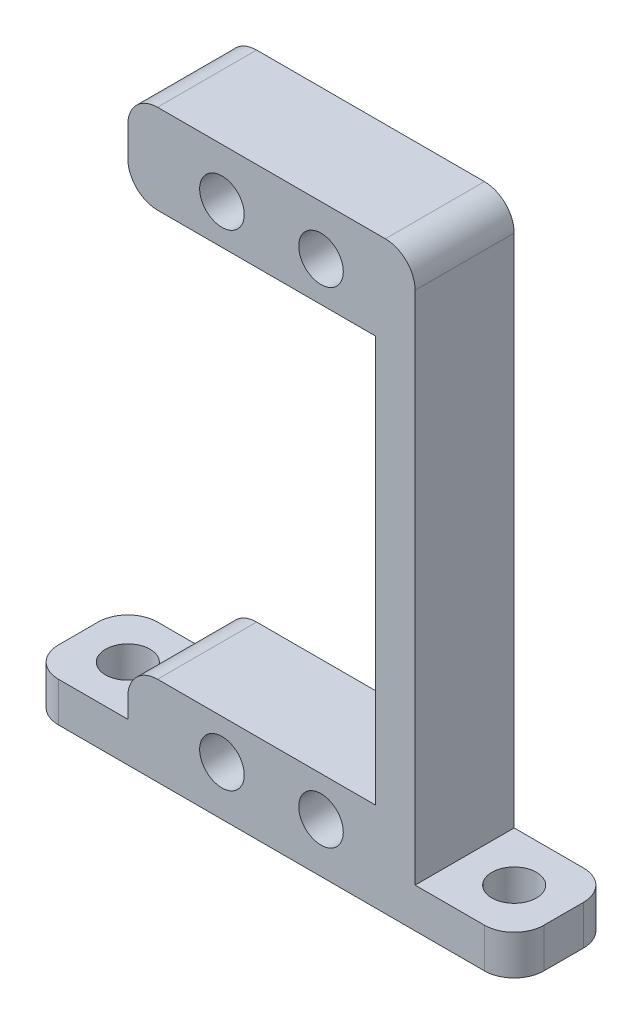
SolidWorks part; units mm, degrees
material "8200树脂"
ref_plane "前视基准面" through (0, 0, 0) normal (0, 0, 1) x (1, 0, 0)
ref_plane "上视基准面" through (0, 0, 0) normal (0, 1, 0) x (1, 0, 0)
ref_plane "右视基准面" through (0, 0, 0) normal (1, 0, 0) x (0, 0, -1)
sketch "草图1" plane through (0, 0, 0) normal (0, 0, 1) x (1, 0, 0)
  line L0 (-10.5, 20.5) -> (-14.5, 20.5)
  line L1 (-10.5, -20.5) -> (10.5, -20.5)
  line L2 (-10.5, -20.5) -> (-10.5, 20.5)
  line L3 (-10.5, 20.5) -> (10.5, 20.5)
  line L4 (10.5, -20.5) -> (10.5, 20.5)
  line L5 (-10.5, -20.5) -> (10.5, 20.5) construction
  line L6 (-10.5, 20.5) -> (10.5, -20.5) construction
  line L7 (-14.5, 20.5) -> (-14.5, 29.5)
  line L8 (-14.5, 29.5) -> (14.5, 29.5)
  line L9 (14.5, 29.5) -> (14.5, -29.5)
  line L10 (14.5, -29.5) -> (-14.5, -29.5)
  line L11 (-14.5, -29.5) -> (-14.5, -20.5)
  line L12 (-14.5, -20.5) -> (-10.5, -20.5)
  line L13 (14.5, -29.5) -> (24.5, -29.5)
  line L14 (24.5, -29.5) -> (24.5, -25.5)
  line L15 (24.5, -25.5) -> (14.5, -25.5)
  line L16 (0, -55) -> (0, 55) construction
  line L17 (-24.5, -29.5) -> (-24.5, -25.5)
  line L18 (-14.5, -29.5) -> (-24.5, -29.5)
  line L19 (-24.5, -25.5) -> (-14.5, -25.5)
  line L20 (55, 0) -> (-55, 0) construction
  circle A0 centre (-5, 24.5) radius 2.25
  circle A1 centre (5, 24.5) radius 2.25
  circle A2 centre (5, -24.5) radius 2.25
  circle A3 centre (-5, -24.5) radius 2.25
  point P0 (0, 0)
  dimension "D10" = 4.5
  dimension "D11" = 10
  dimension "D12" = 49
  dimension "D1" = 21
  dimension "D2" = 41
  dimension "D3" = 9
  dimension "D4" = 9
  dimension "D5" = 4
  dimension "D6" = 4
  dimension "D7" = 4
  dimension "D8" = 4
  dimension "D9" = 10
extrude "凸台-拉伸1" add sketch "草图1" along normal blind 10 contours L19 L17 L18 L11 | L12 L11 L10 L9 L8 L7 L0 L3 L4 L1 A1 A0 A2 A3 | L14 L15 L9 L13
sketch "草图2" plane through (0, -25.5, 0) normal (0, 1, 0) x (1, 0, 0)
  line L0 (24.5, -5) -> (14.5, -5) construction
  line L1 (24.5, -10) -> (24.5, 0) construction
  line L2 (14.5, -10) -> (14.5, 0) construction
  line L3 (0, -5.5) -> (0, 5.5) construction
  circle A0 centre (19.5, -5) radius 2.25
  circle A1 centre (-19.5, -5) radius 2.25
  dimension "D1" = 4.5
extrude "切除-拉伸1" cut sketch "草图2" against normal blind 10
fillet "圆角1" radius 3 8 edges at (-14.5, -20.5, 5) (14.5, 29.5, 5) (-14.5, 20.5, 5) (-14.5, 29.5, 5) (-24.5, -27.5, 0) (-24.5, -27.5, 10) (24.5, -27.5, 0) (24.5, -27.5, 10)
